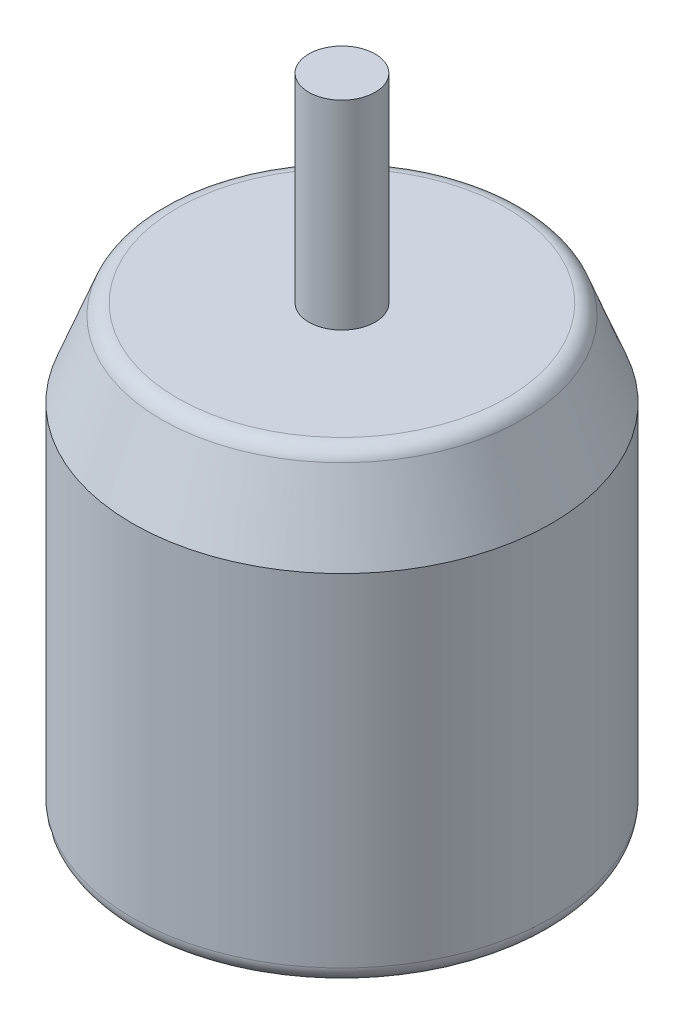
SolidWorks part; units mm, degrees
ref_plane "Front Plane" through (0, 0, 0) normal (0, 0, 1) x (1, 0, 0)
ref_plane "Top Plane" through (0, 0, 0) normal (0, 1, 0) x (1, 0, 0)
ref_plane "Right Plane" through (0, 0, 0) normal (1, 0, 0) x (0, 0, -1)
sketch "Sketch3" plane through (0, 0, 0) normal (0, 1, 0) x (1, 0, 0)
  circle A0 centre (0, 0) radius 31.55
  dimension "D1" = 63.1
extrude "Boss-Extrude1" add sketch "Sketch3" along normal blind 13
sketch "Sketch5" plane through (0, 0, 0) normal (0, 0, 1) x (1, 0, 0)
  line L0 (31.55, 13) -> (26.55, 13)
  line L1 (31.55, 13) -> (-31.55, 13) construction
  line L2 (26.55, 13) -> (31.55, 0)
  line L3 (31.55, 0) -> (31.55, 13)
  dimension "D1" = 5
ref_axis "Axis1" through (0, 13, 0) along (0, -1, 0)
revolve "Cut-Revolve1" cut sketch "Sketch5" angle 360 about axis through (0, 13, 0) along (0, -1, 0)
sketch "Sketch6" plane through (0, 0, 0) normal (0, -1, 0) x (1, 0, 0)
  circle A0 centre (0, 0) radius 31.55
extrude "Boss-Extrude2" add sketch "Sketch6" along normal blind 54
fillet "Fillet1" radius 2.54 2 edges at (0, -54, -31.55) (0, 13, 26.55)
sketch "Sketch7" plane through (0, 13, 0) normal (0, 1, 0) x (1, 0, 0)
  circle A0 centre (0, 0) radius 5
  dimension "D1" = 10
extrude "Boss-Extrude3" add sketch "Sketch7" along normal blind 30
